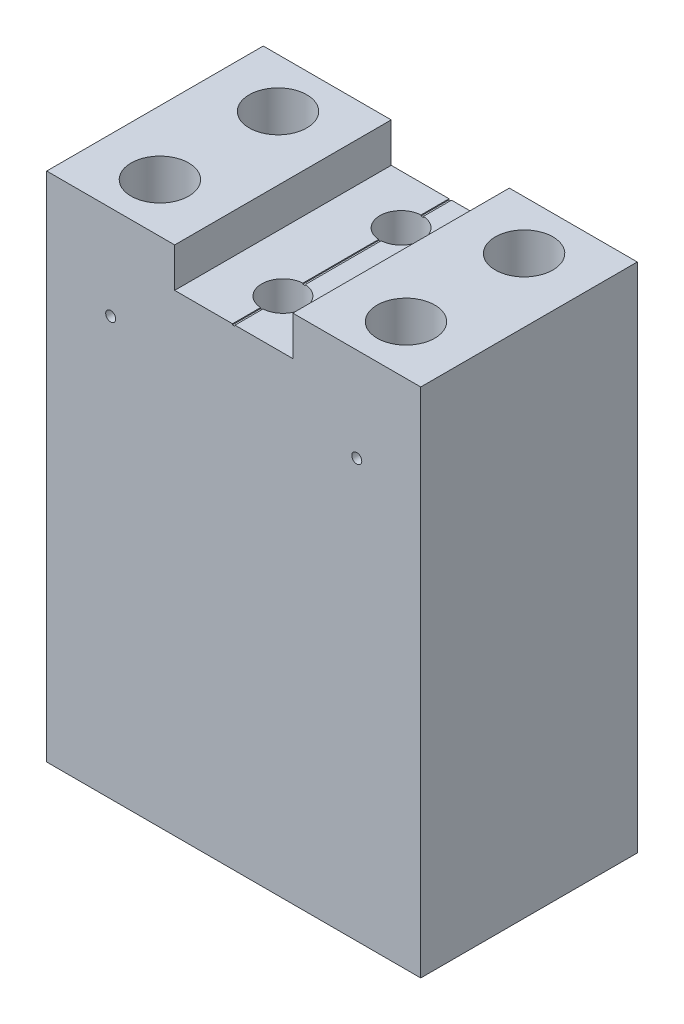
SolidWorks part; units mm, degrees
ref_plane "Front" through (0, 0, 0) normal (0, 0, 1) x (1, 0, 0)
ref_plane "Top" through (0, 0, 0) normal (0, 1, 0) x (1, 0, 0)
ref_plane "Right" through (0, 0, 0) normal (1, 0, 0) x (0, 0, -1)
sketch "Sketch1" plane through (0, 0, 0) normal (0, 0, 1) x (1, 0, 0)
  line L1 (-19, 52) -> (19, 52)
  line L2 (-19, 52) -> (-19, 0)
  line L3 (-19, 0) -> (19, 0)
  line L4 (19, 52) -> (19, 0)
  dimension "D1" = 52
  dimension "D2" = 38
extrude "Extrude1" add sketch "Sketch1" along normal blind 22
sketch "Sketch2" plane through (0, 52, 0) normal (0, 1, 0) x (-1, 0, 0)
  line L0 (19, 11) -> (-19, 11) construction
  line L1 (19, 22) -> (19, 0) construction
  line L2 (-19, 22) -> (-19, 0) construction
  line L3 (0, 0) -> (0, 22) construction
  line L4 (-19, 22) -> (19, 22) construction
  circle A0 centre (12.5, 5) radius 2.925
  circle A1 centre (12.5, 17) radius 2.925
  circle A2 centre (-12.5, 17) radius 2.925
  circle A3 centre (-12.5, 5) radius 2.925
  dimension "D1" = 25
  dimension "D2" = 12
  dimension "D3" = 5.85
extrude "Cut-Extrude1" cut sketch "Sketch2" against normal blind 12.7
sketch "Sketch5" plane through (0, 52, 0) normal (0, 1, 0) x (-1, 0, 0)
  line L0 (-19, 0) -> (19, 0) construction
  line L1 (6, 0) -> (-6, 0)
  line L2 (6, 0) -> (6, 22)
  line L3 (6, 22) -> (-6, 22)
  line L4 (-6, 0) -> (-6, 22)
  line L5 (-19, 22) -> (19, 22) construction
  dimension "D1" = 12
extrude "Cut-Extrude4" cut sketch "Sketch5" against normal blind 4
hole_wizard "#8 Clearance Hole1" positions "Sketch7" profile "Sketch6" hole size "#8" standard "Ansi Inch" end condition through all
sketch "Sketch7" plane through (0, 48, 0) normal (0, 1, 0) x (-1, 0, 0)
  line L0 (6, 11) -> (-6, 11) construction
  line L1 (6, 0) -> (6, 22) construction
  line L2 (-6, 22) -> (-6, 0) construction
  point P0 (0, 17)
  point P1 (0, 5)
  dimension "D1" = 12
sketch "Sketch6" plane through (0, 48, 17) normal (1, 0, 0) x (0, 0, 1)
  line L0 (0, 0) -> (0, 48)
  line L1 (0, 48) -> (2.1526, 48)
  line L2 (2.1526, 48) -> (2.1526, 0)
  line L5 (2.1526, 0) -> (0, 0)
  line L11 (0, -6.35) -> (0, 107.95) construction
  dimension "Thru Hole Dia." = 4.3053
  dimension "Thru Hole Depth" = 48
sketch "Sketch8" plane through (0, 0, 22) normal (0, 0, 1) x (1, 0, 0)
  line L0 (-12.5, 52) -> (-12.5, 42.475) construction
  line L1 (-6, 52) -> (-19, 52) construction
  line L2 (0, 54.681) -> (0, 31.9157) construction
  circle A0 centre (-12.5, 42.475) radius 0.508
  circle A1 centre (12.5, 42.475) radius 0.508
  dimension "D1" = 1.016
  dimension "D2" = 9.525
extrude "Cut-Extrude5" cut sketch "Sketch8" against normal up to next
mirror "Mirror1" about plane through (0, 0, 0) normal (0, 0, 1) of "Cut-Extrude5"
sketch "Sketch9" plane through (0, 48, 0) normal (0, 1, 0) x (-1, 0, 0)
  line L0 (-6, 0) -> (6, 0) construction
  line L1 (0.125, 0) -> (-0.125, 0)
  line L2 (0.125, 0) -> (0.125, 22)
  line L3 (0.125, 22) -> (-0.125, 22)
  line L4 (-0.125, 0) -> (-0.125, 22)
  dimension "D1" = 0.25
extrude "Cut-Extrude6" cut sketch "Sketch9" against normal blind 0.1
